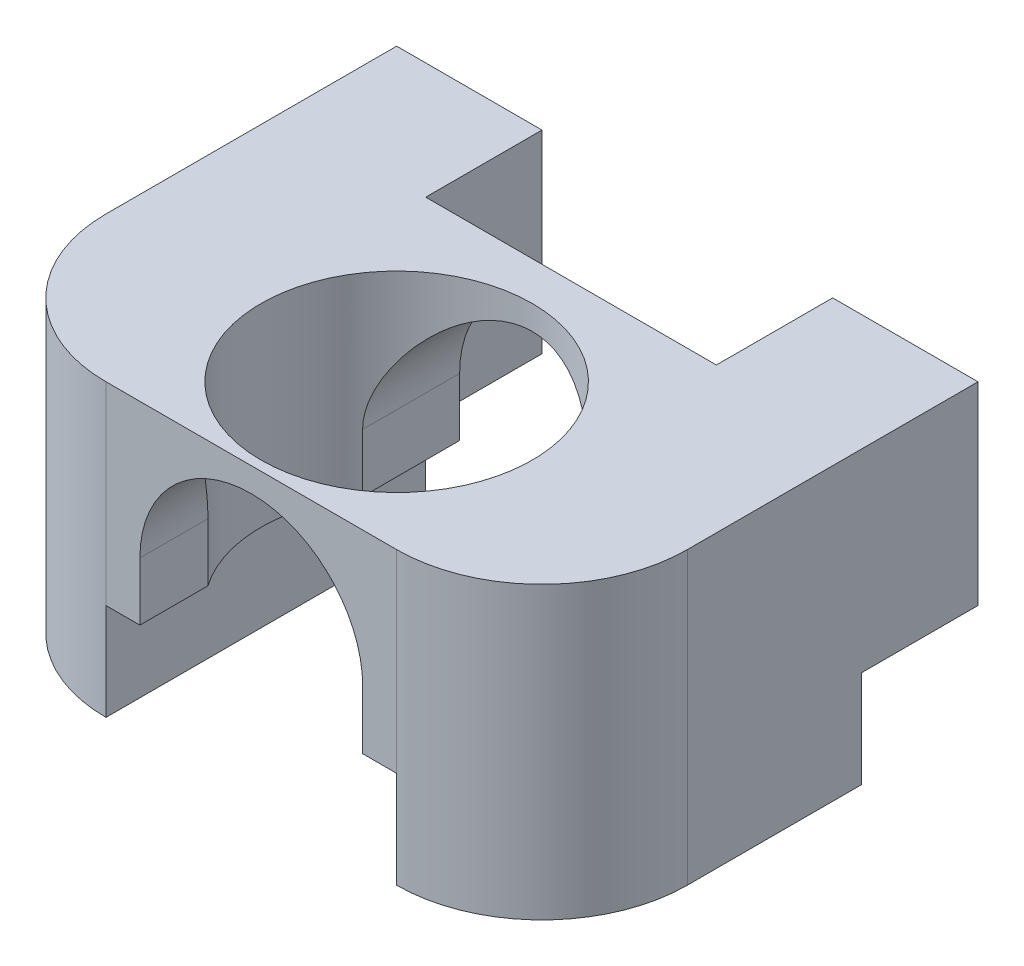
SolidWorks part; units mm, degrees
ref_plane "Front Plane" through (0, 0, 0) normal (0, 0, 1) x (1, 0, 0)
ref_plane "Top Plane" through (0, 0, 0) normal (0, 1, 0) x (1, 0, 0)
ref_plane "Right Plane" through (0, 0, 0) normal (1, 0, 0) x (0, 0, -1)
sketch "Sketch1" plane through (0, 0, 0) normal (0, 0, 1) x (1, 0, 0)
  line L0 (0, -16) -> (15, -16) construction
  line L1 (0, -6) -> (15, -6) construction
  line L2 (15, -6) -> (15, -16) construction
  line L3 (0, 0) -> (0, -16) construction
  circle A0 centre (0, 0) radius 11.5
  point P7 (0, -6.6902)
  dimension "D1" = 23
  dimension "D2" = 16
  dimension "D3" = 10
  dimension "D4" = 15
sketch "Sketch2" plane through (0, 0, 0) normal (0, 0, 1) x (1, 0, 0)
  line L0 (-11.5, 0) -> (11.5, 0) construction
  line L1 (11.5, 0) -> (11.5, -6)
  line L2 (0, -6) -> (15, -6) construction
  line L3 (11.5, -6) -> (15, -6)
  line L4 (-11.5, 0) -> (-11.5, -6)
  line L5 (-11.5, -6) -> (-15, -6)
  line L6 (-15, -6) -> (-15, 14)
  line L7 (-15, 14) -> (15, 14)
  line L8 (15, 14) -> (15, -6)
  arc A0 (11.5, 0) -> (-11.5, 0) centre (0, 0) ccw
  circle A1 centre (0, 0) radius 11.5 construction
  dimension "D1" = 20
extrude "Boss-Extrude1" add sketch "Sketch2" along normal blind 33
sketch "Sketch3" plane through (0, 14, 0) normal (0, 1, 0) x (1, 0, 0)
  line L0 (-15, -18) -> (15, -18) construction
  line L1 (-15, -33) -> (-15, 0) construction
  line L2 (15, -33) -> (15, 0) construction
  line L3 (15, -33) -> (-15, -33) construction
  circle A0 centre (0, -18) radius 14
  dimension "D1" = 28
  dimension "D2" = 15
extrude "Cut-Extrude1" cut sketch "Sketch3" against normal through all
sketch "Sketch4" plane through (0, 14, 0) normal (0, 1, 0) x (1, 0, 0)
  line L0 (15, 0) -> (-15, 0) construction
  line L1 (15, -33) -> (30, -33)
  line L2 (15, -33) -> (15, 12)
  line L3 (15, 12) -> (30, 12)
  line L4 (30, -33) -> (30, 12)
  dimension "D1" = 15
  dimension "D2" = 12
extrude "Boss-Extrude2" add sketch "Sketch4" against normal up to surface (20 mm away) up to face at (13.0833, -6, 17)
hole_wizard "M5x0.8 Tapped Hole1" positions "Sketch5" profile "Sketch6" tap size "M5x0.8" standard "ANSI Metric"
sketch "Sketch5" plane through (0, -6, 0) normal (0, -1, 0) x (-1, 0, 0)
  line L0 (-15, 0) -> (-15, 12) construction
  line L1 (0, 0) -> (-15, 0) construction
  point P0 (-24, 6)
  point P5 (-24, 7.7723)
  dimension "D1" = 9
  dimension "D2" = 6
sketch "Sketch6" plane through (24, -6, -6) normal (1, 0, 0) x (0, 0, -1)
  line L0 (0, 0) -> (0, 13.6618)
  line L1 (0, 13.6618) -> (2.1, 12.4)
  line L2 (2.1, 12.4) -> (2.1, 0)
  line L5 (2.1, 0) -> (0, 0)
  line L10 (0, 13.6618) -> (-2.1, 12.4) construction
  line L11 (0, -6.35) -> (0, 107.95) construction
  dimension "Tap Drill Dia." = 4.2
  dimension "Tap Drill Depth" = 12.4
  dimension "Drill Angle" = 118
cosmetic thread "Hole Thread1" parameters "D1"=10, "D2"=5
sketch "Sketch7" plane through (0, -6, 0) normal (0, -1, 0) x (1, 0, 0)
  line L1 (15, 0) -> (30, 0)
  line L2 (15, 0) -> (15, 33)
  line L3 (15, 33) -> (30, 33)
  line L4 (30, 0) -> (30, 33)
extrude "Boss-Extrude3" add sketch "Sketch7" along normal blind 10
mirror "Mirror1" about plane through (0, 0, 0) normal (1, 0, 0) of "M5x0.8 Tapped Hole1", "Boss-Extrude2", "Boss-Extrude3"
cosmetic thread "Hole Thread2" parameters "D1"=10, "D2"=5
fillet "Fillet1" radius 15 2 edges at (30, -1, 33) (-30, -1, 33)
